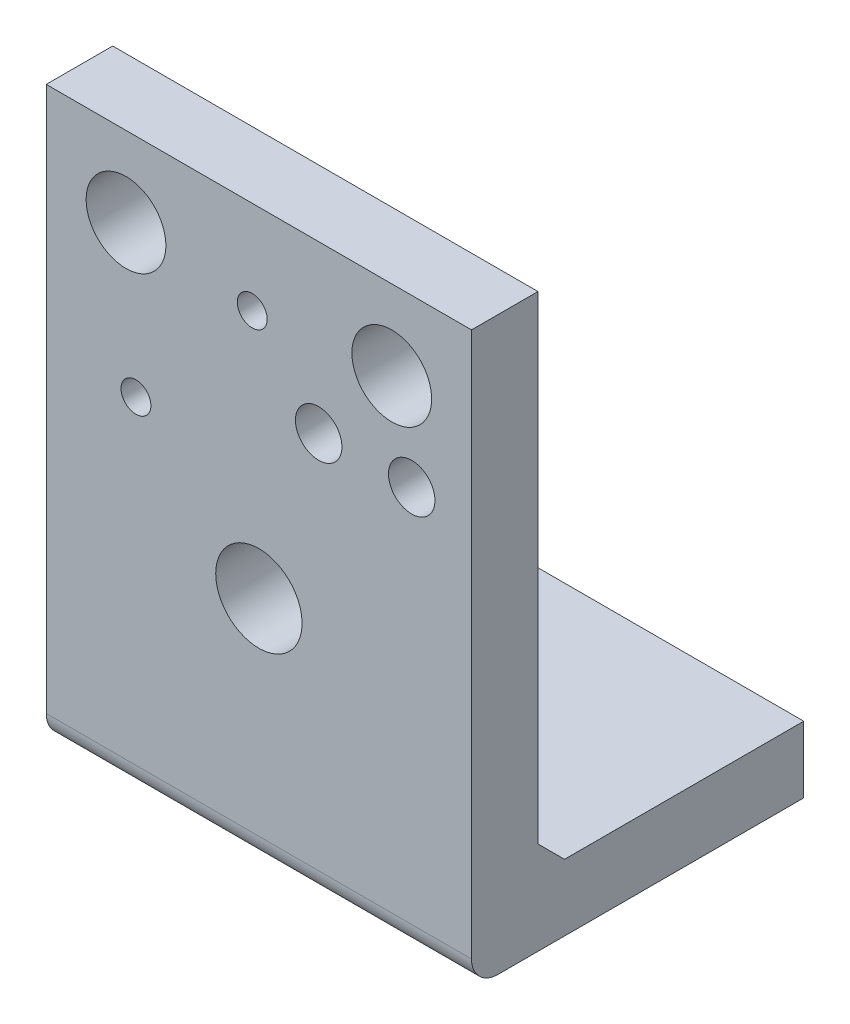
SolidWorks part; units mm, degrees
ref_plane "Front Plane" through (0, 0, 0) normal (0, 0, 1) x (1, 0, 0)
ref_plane "Top Plane" through (0, 0, 0) normal (0, 1, 0) x (1, 0, 0)
ref_plane "Right Plane" through (0, 0, 0) normal (1, 0, 0) x (0, 0, -1)
sketch "Sketch1" plane through (0, 0, 0) normal (0, 0, 1) x (1, 0, 0)
  line L1 (-32, 43) -> (32, 43)
  line L2 (-32, 43) -> (-32, -43)
  line L3 (-32, -43) -> (32, -43)
  line L4 (32, 43) -> (32, -43)
  line L5 (-32, 43) -> (32, -43) construction
  line L6 (-32, -43) -> (32, 43) construction
  point P0 (0, 0)
  dimension "D1" = 86
  dimension "D2" = 64
extrude "Boss-Extrude1" add sketch "Sketch1" along normal blind 10
sketch "Sketch2" plane through (0, 0, 0) normal (0, 0, -1) x (-1, 0, 0)
  line L0 (32, 43) -> (32, -43) construction
  line L1 (-32, -43) -> (32, -43)
  line L2 (-32, -43) -> (-32, -33)
  line L3 (-32, -33) -> (32, -33)
  line L4 (32, -43) -> (32, -33)
  dimension "D1" = 10
extrude "Boss-Extrude2" add sketch "Sketch2" along normal blind 40
sketch "Sketch3" plane through (0, 0, 0) normal (1, 0, 0) x (0, 0, -1)
  line L0 (40, -33) -> (0, -25)
  line L1 (0, -25) -> (0, -33)
  line L2 (0, -33) -> (40, -33)
  line L3 (0, -25) -> (0, 43) construction
  dimension "D1" = 68
sketch "Sketch4" plane through (0, 0, 0) normal (0, 0, -1) x (-1, 0, 0)
  line L0 (32, 43) -> (32, -43) construction
  line L1 (-32, 43) -> (32, 43) construction
  circle A0 centre (20, 31) radius 6
  circle A1 centre (1, 29) radius 2.25
  circle A2 centre (-20, 31) radius 6
  circle A3 centre (-9, 18) radius 3.5
  circle A4 centre (-23, 18) radius 3.5
  circle A5 centre (18.5, 9) radius 2.25
  circle A6 centre (0, -8) radius 6.5
  dimension "D15" = 12
  dimension "D16" = 12
  dimension "D17" = 4.5
  dimension "D18" = 7
  dimension "D19" = 7
  dimension "D20" = 13
  dimension "D21" = 4.5
  dimension "D1" = 12
  dimension "D2" = 12
  dimension "D3" = 14
  dimension "D4" = 31
  dimension "D5" = 52
  dimension "D6" = 12
  dimension "D7" = 32
  dimension "D8" = 51
  dimension "D9" = 13.5
  dimension "D10" = 34
  dimension "D11" = 25
  dimension "D12" = 41
  dimension "D13" = 55
  dimension "D14" = 25
extrude "Cut-Extrude1" cut sketch "Sketch4" against normal through all
ref_plane "Plane1" through (-32, 0, 0) normal (-1, 0, 0) x (0, 0, 1)
sketch "Sketch5" plane through (-32, 0, 0) normal (-1, 0, 0) x (0, 0, 1)
  line L0 (-40, -33) -> (-40, 61)
  line L1 (-40, 61) -> (10, 61)
  line L2 (10, 61) -> (10, 43)
  line L3 (10, 43) -> (0, 43)
  line L4 (0, 43) -> (0, 51)
  line L5 (0, 51) -> (-27, 51)
  line L6 (-27, 51) -> (-27, -33)
  line L7 (-27, -33) -> (-40, -33)
  line L8 (-40, -43) -> (-40, -33) construction
  dimension "D1" = 37
  dimension "D2" = 8
  dimension "D3" = 10
sketch "Sketch6" plane through (0, -33, 0) normal (0, 1, 0) x (1, 0, 0)
  line L0 (32, 0) -> (-32, 0) construction
  line L1 (0, -27.5) -> (0, 27.5) construction
  line L3 (-5.25, 11.25) -> (5.25, 11.25) construction
  line L4 (-5.25, 11.25) -> (-5.25, 21.75) construction
  line L5 (-5.25, 21.75) -> (5.25, 21.75) construction
  line L6 (5.25, 11.25) -> (5.25, 21.75) construction
  line L7 (-5.25, 11.25) -> (5.25, 21.75) construction
  line L8 (-5.25, 21.75) -> (5.25, 11.25) construction
  line L9 (0, 6.9541) -> (-9.5459, 16.5) construction
  line L10 (0, 6.9541) -> (9.5459, 16.5) construction
  line L11 (9.5459, 16.5) -> (0, 26.0459) construction
  line L12 (-9.5459, 16.5) -> (0, 26.0459) construction
  line L13 (0, 6.9541) -> (0, 26.0459) construction
  line L14 (9.5459, 16.5) -> (-9.5459, 16.5) construction
  circle A0 centre (0, 16.5) radius 2
  circle A1 centre (5.25, 21.75) radius 1.25
  circle A2 centre (5.25, 11.25) radius 1.25
  circle A3 centre (-5.25, 11.25) radius 1.25
  circle A4 centre (-5.25, 21.75) radius 1.25
  circle A5 centre (-9.5459, 16.5) radius 2
  circle A6 centre (0, 6.9541) radius 2
  circle A7 centre (9.5459, 16.5) radius 2
  circle A8 centre (0, 26.0459) radius 2
  point P6 (5.25, 16.5)
  dimension "D2" = 4
  dimension "D3" = 2.5
  dimension "D7" = 4
  dimension "D1" = 16.5
  dimension "D4" = 10.5
  dimension "D5" = 10.5
  dimension "D6" = 13.5
extrude "Cut-Extrude2" cut sketch "Sketch6" against normal through all
chamfer "Chamfer1" distance 4 angle 45 1 edges at (0, -33, 0)
fillet "Fillet1" radius 4 1 edges at (0, -43, 10)
